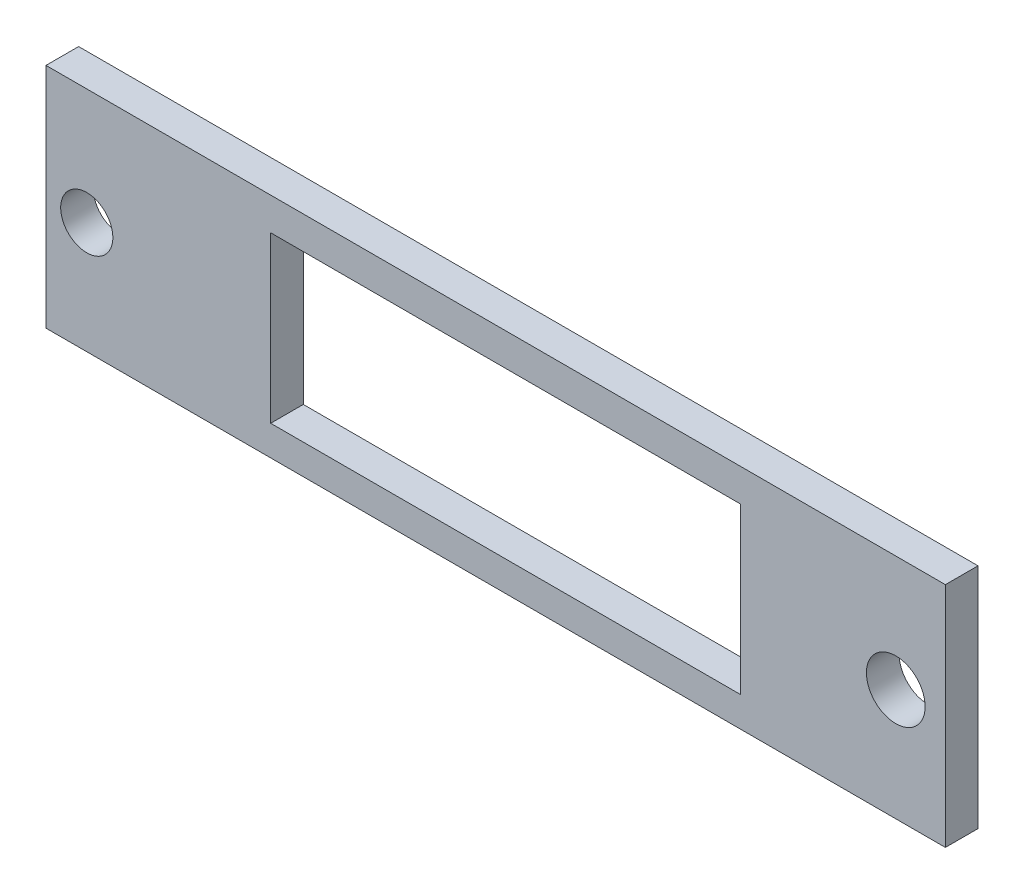
SolidWorks part; units mm, degrees
ref_plane "Front Plane" through (0, 0, 0) normal (0, 0, 1) x (1, 0, 0)
ref_plane "Top Plane" through (0, 0, 0) normal (0, 1, 0) x (1, 0, 0)
ref_plane "Right Plane" through (0, 0, 0) normal (1, 0, 0) x (0, 0, -1)
sketch "Sketch1" plane through (0, 0, 0) normal (0, 0, 1) x (1, 0, 0)
  line L0 (-27.3, 6.9) -> (-27.3, -7.055)
  line L2 (-27.5, 7.1) -> (-27.5, -7.255)
  line L3 (-27.5, -7.255) -> (28.0417, -7.255)
  line L5 (-27.3, -7.055) -> (27.8417, -7.055)
  line L6 (27.8417, 6.9) -> (27.8417, -7.055)
  line L7 (-27.3, 6.9) -> (27.8417, 6.9)
  line L8 (28.0417, 7.1) -> (28.0417, -7.255) construction
  line L9 (-27.5, 7.1) -> (28.0417, 7.1) construction
  line L10 (0.2708, 6.9) -> (0.2708, 4.9)
  line L11 (0.2708, 4.9) -> (15.2708, 4.9)
  line L13 (15.2708, 4.9) -> (-13.5247, 4.9)
  line L14 (15.2708, 4.9) -> (15.2708, -5.2158)
  line L15 (15.2708, -5.2158) -> (-13.5247, -5.2158)
  line L16 (-13.5247, 4.9) -> (-13.5247, -5.2158)
  circle A2 centre (24.8, -0.2) radius 1.8
  circle A3 centre (24.8, -0.2) radius 1.8
  circle A5 centre (-24.8, -0.2) radius 1.6
  circle A6 centre (-24.8, -0.2) radius 1.6
  dimension "D1" = 0.2
  dimension "D2" = 0.2
  dimension "D3" = 0.2
extrude "Boss-Extrude1" add sketch "Sketch1" along normal blind 2
